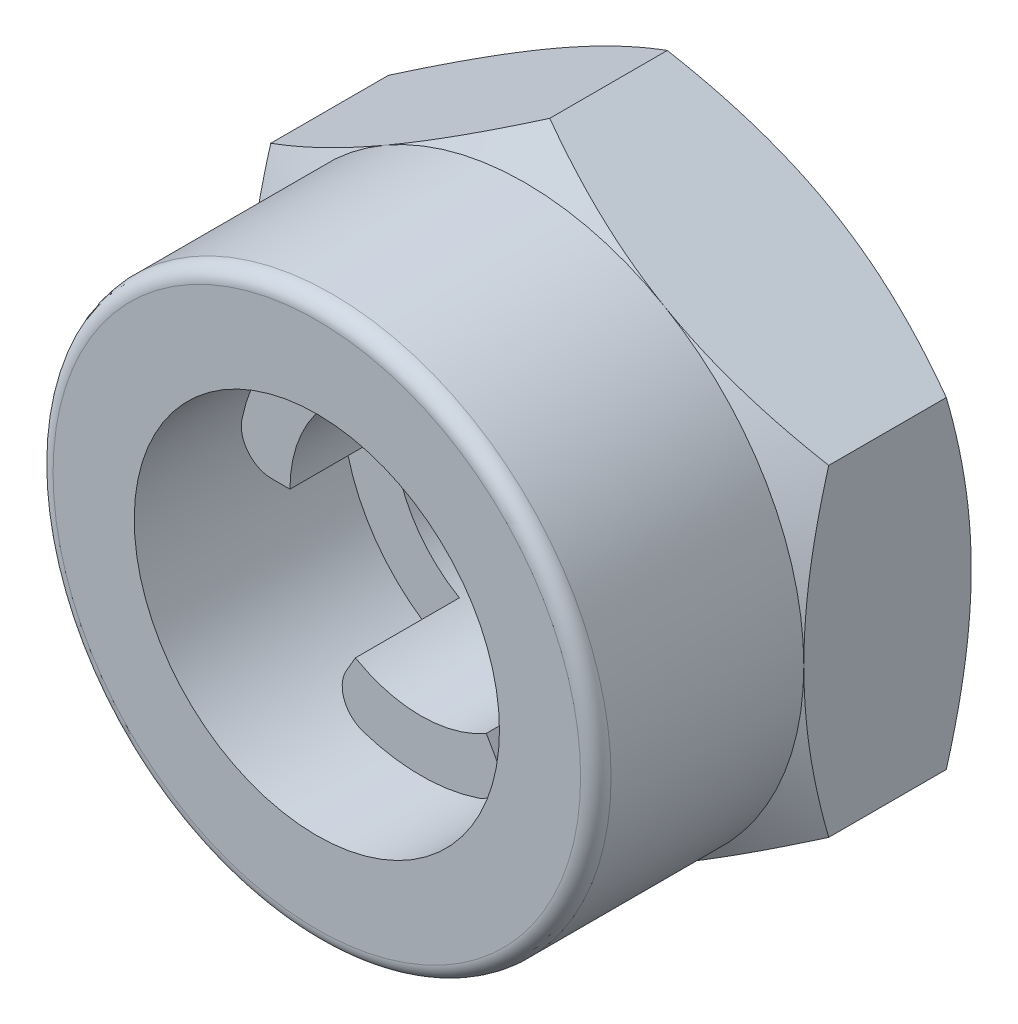
SolidWorks part; units mm, degrees
ref_plane "前视基准面" through (0, 0, 0) normal (0, 0, 1) x (1, 0, 0)
ref_plane "上视基准面" through (0, 0, 0) normal (0, 1, 0) x (1, 0, 0)
ref_plane "右视基准面" through (0, 0, 0) normal (1, 0, 0) x (0, 0, -1)
sketch "草图1" plane through (0, 0, 0) normal (0, 0, 1) x (1, 0, 0)
  line L1 (0, 3.1754) -> (-2.75, 1.5877)
  line L2 (-2.75, 1.5877) -> (-2.75, -1.5877)
  line L3 (-2.75, -1.5877) -> (0, -3.1754)
  line L4 (0, -3.1754) -> (2.75, -1.5877)
  line L5 (2.75, -1.5877) -> (2.75, 1.5877)
  line L6 (2.75, 1.5877) -> (0, 3.1754)
  circle A0 centre (0, 0) radius 2.75 construction
  circle A1 centre (0, 0) radius 1.29
  dimension "D1" = 2.58
  dimension "D2" = 5.5
extrude "凸台-拉伸1" add sketch "草图1" against normal blind 1.65
cosmetic thread "装饰螺纹线1" parameters "D1"=15, "D2"=22
sketch "草图2" plane through (0, 0, 0) normal (1, 0, 0) x (0, 0, -1)
  line L0 (0, 2.75) -> (0.2456, 3.1754)
  line L1 (0, 1.5877) -> (0, 3.1754) construction
  line L2 (1.65, 3.1754) -> (0, 3.1754) construction
  line L3 (0.2456, 3.1754) -> (0, 3.1754)
  line L4 (0, 3.1754) -> (0, 2.75)
  line L5 (0, 0) -> (1.65, 0) construction
  line L6 (1.65, -1.5877) -> (1.65, 1.5877) construction
  line L7 (1.65, 2.75) -> (1.4044, 3.1754)
  line L8 (1.65, 1.5877) -> (1.65, 3.1754) construction
  line L9 (1.4044, 3.1754) -> (1.65, 3.1754)
  line L10 (1.65, 3.1754) -> (1.65, 2.75)
  dimension "D1" = 5.5
  dimension "D2" = 30
revolve "切除-旋转1" cut sketch "草图2" angle 360 about L5
chamfer "倒角1" distance 0.15 angle 45 1 edges at (1.29, 0, -1.65)
sketch "草图3" plane through (0, 0, 0) normal (0, 0, 1) x (1, 0, 0)
  circle A0 centre (0, 0) radius 1.8
  circle A1 centre (0, 0) radius 2.75
  dimension "D1" = 3.6
extrude "凸台-拉伸2" add sketch "草图3" along normal blind 2.05
fillet "圆角1" radius 0.15 1 edges at (2.75, 0, 2.05)
sketch "草图4" plane through (0, 0, 0) normal (0, 0, 1) x (1, 0, 0)
  line L0 (-1.29, 0) -> (-1.4697, 0)
  line L1 (-0.645, 1.1172) -> (-0.7348, 1.2728)
  arc A0 (-1.4697, 0) -> (-1.7636, 0.36) centre (-1.4697, 0.3) cw
  arc A1 (-1.1936, 1.3474) -> (-0.7348, 1.2728) centre (-0.9947, 1.1228) cw
  circle A3 centre (0, 0) radius 1.8 construction
  arc A4 (-1.1936, 1.3474) -> (-1.7636, 0.36) centre (0, 0) ccw
  arc A5 (-0.645, 1.1172) -> (-1.29, 0) centre (0, 0) ccw
  point P4 (-1.8, 0)
  dimension "D1" = 2.58
  dimension "D3" = 0.3
  dimension "D2" = 60
extrude "凸台-拉伸3" add sketch "草图4" along normal blind 1.025
pattern_circular "阵列(圆周)1" count 3 over 360 about axis through (0, 0, 0) along (0, 0, 1) of "凸台-拉伸3"
sketch "草图5" plane through (0, 0, -1.65) normal (0, 0, -1) x (-1, 0, 0)
  circle A0 centre (0, 0) radius 2.75
  circle A2 centre (0, 0) radius 1.65
  dimension "D1" = 3.3
extrude "凸台-拉伸4" [suppressed] add sketch "草图5" along normal blind 2.05
fillet "圆角2" [suppressed] radius 0.36
sketch "草图6" [suppressed] plane through (0, 0, -22) normal (0, 0, -1) x (-1, 0, 0)
  circle A0 centre (0, 0) radius 13.75
  dimension "D1" = 3.75
extrude "切除-拉伸1" [suppressed] cut sketch "草图6" against normal blind 0.5125
chamfer "倒角2" [suppressed] distance 0.15 angle 45
